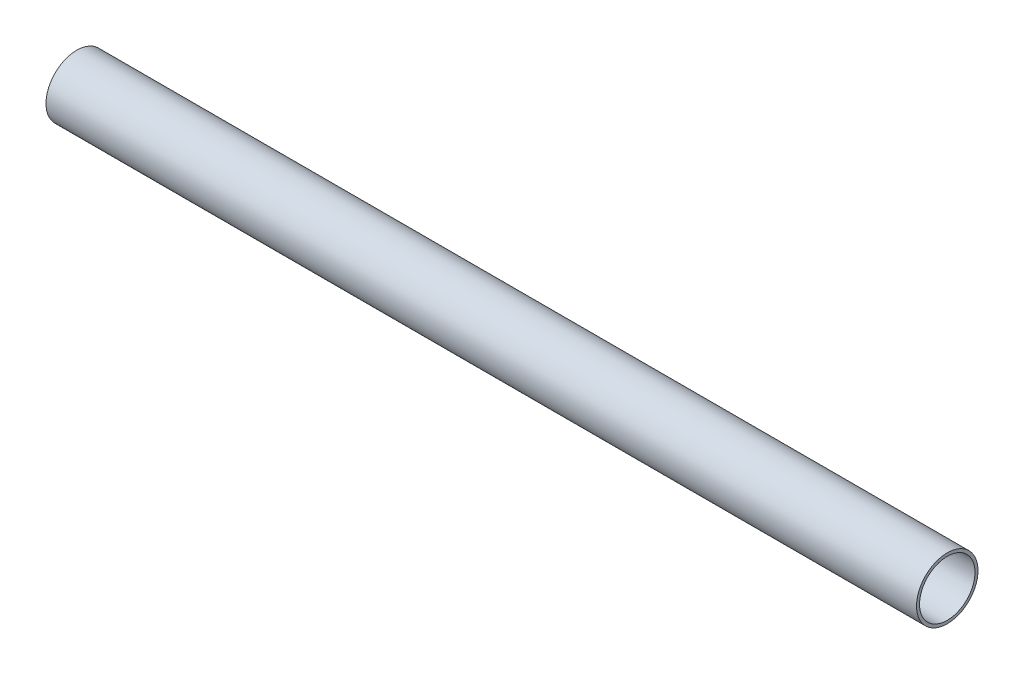
SolidWorks part; units mm, degrees
material "AISI 4130 Steel, normalized at 870C"
ref_plane "Front Plane" through (0, 0, 0) normal (0, 0, 1) x (1, 0, 0)
ref_plane "Top Plane" through (0, 0, 0) normal (0, 1, 0) x (1, 0, 0)
ref_plane "Right Plane" through (0, 0, 0) normal (1, 0, 0) x (0, 0, -1)
sketch "Sketch1" plane through (0, 0, 0) normal (0, 0, 1) x (1, 0, 0)
  line L0 (-766.2482, -0.0004) -> (-582.5982, -0.0004) construction
  line L2 (-770.8982, -6.0004) -> (-770.8982, -6.6504)
  line L3 (-770.8982, -6.6504) -> (-582.5982, -6.6504)
  line L4 (-582.5982, -6.0004) -> (-582.5982, -6.6504)
  line L7 (-766.2482, -0.0004) -> (-582.5982, -0.0004) construction
  line L8 (-770.8982, -6.0004) -> (-582.5982, -6.0004)
  line L9 (-770.8982, -6.7504) -> (-770.8982, 6.7496) construction
  point P0 (-674.4232, -0.0004)
  dimension "BAREL OD" = 13.3
  dimension "BAREL ID" = 12
revolve "Revolve1" add sketch "Sketch1" angle 360 about L0
